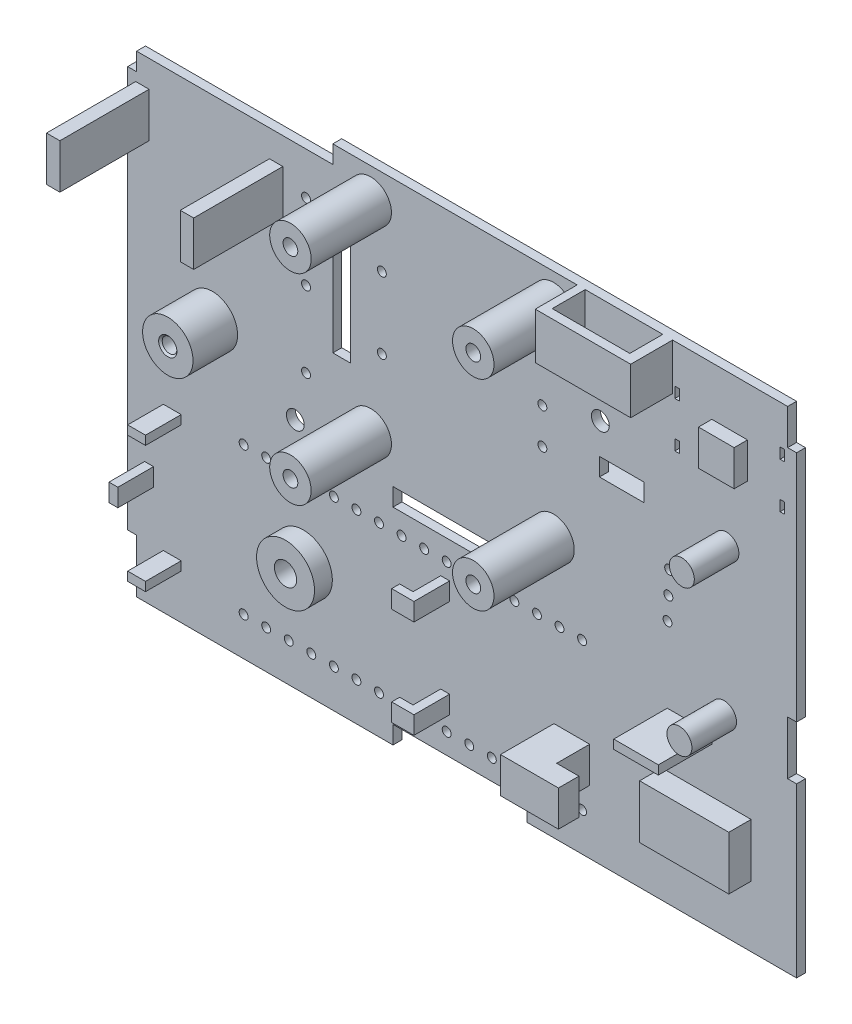
SolidWorks part; units mm, degrees
material "PLA"
ref_plane "前视基准面" through (0, 0, 0) normal (0, 0, 1) x (1, 0, 0)
ref_plane "上视基准面" through (0, 0, 0) normal (0, 1, 0) x (1, 0, 0)
ref_plane "右视基准面" through (0, 0, 0) normal (1, 0, 0) x (0, 0, -1)
sketch "草图1" plane through (0, 0, 0) normal (0, 0, 1) x (1, 0, 0)
  line L1 (-37.5, 27.5) -> (37.5, 27.5)
  line L2 (-37.5, 27.5) -> (-37.5, -27.5)
  line L3 (-37.5, -27.5) -> (37.5, -27.5)
  line L4 (37.5, 27.5) -> (37.5, -27.5)
  line L5 (-37.5, 27.5) -> (37.5, -27.5) construction
  line L6 (-37.5, -27.5) -> (37.5, 27.5) construction
  point P0 (0, 0)
  dimension "D1" = 55
  dimension "D2" = 75
extrude "凸台-拉伸1" add sketch "草图1" along normal blind 1
sketch "草图2" plane through (0, 0, 0) normal (0, 0, -1) x (-1, 0, 0)
  line L1 (-22.7477, 10.1) -> (-13.0477, 10.1)
  line L2 (-22.7477, 10.1) -> (-22.7477, 8.6)
  line L3 (-22.7477, 8.6) -> (-13.0477, 8.6)
  line L4 (-13.0477, 10.1) -> (-13.0477, 8.6)
  line L6 (31, -4.4) -> (-15.5, -4.4) construction
  line L7 (-14.1477, 1.6) -> (-14.1477, 8.6) construction
  line L8 (-21.6477, 1.6) -> (-21.6477, 8.6) construction
  dimension "D1" = 1.1
  dimension "D2" = 1.5
  dimension "D3" = 1.1
  dimension "D4" = 13
extrude "电源凸台-拉伸2" add sketch "草图2" along normal blind 7.1
sketch "草图4" plane through (0, 8.6, 0) normal (0, -1, 0) x (1, 0, 0)
  line L5 (16.1977, -2.8) -> (17.1977, -2.8)
  line L6 (16.1977, -2.8) -> (16.1977, -3.8)
  line L7 (16.1977, -3.8) -> (17.1977, -3.8)
  line L8 (17.1977, -2.8) -> (17.1977, -3.8)
  line L11 (17.8977, -7.1) -> (17.8977, 0) construction
  line L18 (22.7477, -7.1) -> (13.0477, -7.1) construction
  line L19 (-37.5, 0) -> (37.5, 0) construction
  line L20 (18.5977, -2.8) -> (18.5977, -3.8)
  line L21 (19.5977, -3.8) -> (18.5977, -3.8)
  line L22 (19.5977, -2.8) -> (19.5977, -3.8)
  line L23 (19.5977, -2.8) -> (18.5977, -2.8)
  dimension "D1" = 1
  dimension "D2" = 1
  dimension "D3" = 3.4
  dimension "D4" = 2.8
extrude "电源切除-拉伸1" cut sketch "草图4" against normal up to next
sketch "草图5" plane through (0, 0, 0) normal (0, 0, -1) x (-1, 0, 0)
  line L1 (-20.3977, 12.1) -> (-15.3977, 12.1)
  line L2 (-20.3977, 12.1) -> (-20.3977, 10.1)
  line L3 (-20.3977, 10.1) -> (-15.3977, 10.1)
  line L4 (-15.3977, 12.1) -> (-15.3977, 10.1)
  line L6 (-13.0477, 10.1) -> (-22.7477, 10.1) construction
  line L7 (-17.8977, 8.6) -> (-17.8977, 10.1) construction
  line L8 (-22.7477, 8.6) -> (-13.0477, 8.6) construction
  dimension "D1" = 2
  dimension "D2" = 5
extrude "电源线切除-拉伸2" cut sketch "草图5" against normal up to next
sketch "草图9" plane through (0, 0, 0) normal (0, 0, -1) x (-1, 0, 0)
  circle A3 centre (28, 3.6) radius 0.825
  dimension "D1" = 1.65
extrude "DH11拉伸-薄壁1" add sketch "草图9" along normal up to surface (5 mm away) from surface at -1 separate body thin
sketch "草图36" plane through (0, 0, 1) normal (0, 0, 1) x (1, 0, 0)
  line L0 (-21.7, -3.9) -> (-21.7, 24.5) construction
  line L1 (-21.6, 22.5) -> (-20.1, 22.5)
  line L2 (-21.6, 22.5) -> (-21.6, 17.5)
  line L3 (-21.6, 17.5) -> (-20.1, 17.5)
  line L4 (-20.1, 22.5) -> (-20.1, 17.5)
  line L5 (-36.6, 22.5) -> (-35.1, 22.5)
  line L6 (-36.6, 22.5) -> (-36.6, 17.5)
  line L7 (-36.6, 17.5) -> (-35.1, 17.5)
  line L8 (-35.1, 22.5) -> (-35.1, 17.5)
  line L9 (-21.7, 24.5) -> (-22.35, 24.5) construction
  line L10 (-35, 24.5) -> (-35, -3.9) construction
  dimension "D1" = 5
  dimension "D2" = 0.1
  dimension "D3" = 2
  dimension "D4" = 1.5
  dimension "D5" = 0.1
extrude "DH11凸台-拉伸11" add sketch "草图36" along normal blind 10
chamfer "HD11倒角3" distance 0.2 angle 45 1 edges at (-27.175, 3.6, 6)
sketch "草图13" plane through (0, 0, 0) normal (0, 0, -1) x (-1, 0, 0)
  line L0 (-24.35, 23.15) -> (-23.85, 23.15)
  line L1 (-36.15, 23.15) -> (-35.65, 23.15)
  line L2 (-36.15, 23.15) -> (-36.15, 21.95)
  line L3 (-36.15, 21.95) -> (-35.65, 21.95)
  line L4 (-35.65, 23.15) -> (-35.65, 21.95)
  line L7 (-24.35, 23.15) -> (-24.35, 21.95)
  line L8 (-24.35, 21.95) -> (-23.85, 21.95)
  line L9 (-23.85, 23.15) -> (-23.85, 21.95)
  line L10 (-24.35, 18.05) -> (-23.85, 18.05)
  line L11 (-24.35, 18.05) -> (-24.35, 16.85)
  line L12 (-24.35, 16.85) -> (-23.85, 16.85)
  line L13 (-23.85, 18.05) -> (-23.85, 16.85)
  line L14 (-36.15, 18.05) -> (-35.65, 18.05)
  line L15 (-36.15, 18.05) -> (-36.15, 16.85)
  line L16 (-36.15, 16.85) -> (-35.65, 16.85)
  line L17 (-35.65, 18.05) -> (-35.65, 16.85)
  line L18 (-36, 23) -> (-36, 22.1) construction
  line L19 (-35.8, 23) -> (-36, 23) construction
  dimension "D1" = 1.2
  dimension "D2" = 0.5
  dimension "D3" = 0.15
  dimension "D4" = 0.15
  dimension "D5" = 2
  dimension "D6" = 2
extrude "按键切除-拉伸3" cut sketch "草图13" against normal up to next (1 mm away)
sketch "草图35" plane through (0, 0, 0) normal (0, 0, -1) x (-1, 0, 0)
  line L0 (-35.65, 18.05) -> (-35.65, 21.95) construction
  line L1 (-32, 22) -> (-28, 22)
  line L2 (-32, 22) -> (-32, 18)
  line L3 (-32, 18) -> (-28, 18)
  line L4 (-28, 22) -> (-28, 18)
  line L5 (-30, 18.05) -> (-30, 23.8585) construction
  line L6 (-35.65, 18.05) -> (-24.35, 18.05) construction
  line L7 (-35.65, 20) -> (-24.0484, 20) construction
  line L8 (-24.35, 18.05) -> (-24.35, 16.85) construction
  point P11 (-30, 18.05)
  dimension "D1" = 4
  dimension "D2" = 4
extrude "按键凸台-拉伸10" add sketch "草图35" against normal up to surface (2.5 mm away)
sketch "草图18" plane through (0, 0, 0) normal (0, 0, -1) x (-1, 0, 0)
  circle A0 centre (17.8, -14.8882) radius 1.25
  dimension "D1" = 2.5
extrude "蜂鸣拉伸-薄壁9" add sketch "草图18" along normal up to surface (2 mm away) from surface at -1 separate body thin
sketch "草图38" plane through (0, 0, 1) normal (0, 0, 1) x (1, 0, 0)
  line L1 (-2.4, -8.3882) -> (-1.4, -8.3882)
  line L2 (-2.4, -8.3882) -> (-2.4, -10.3882)
  line L3 (-2.4, -10.3882) -> (-1.4, -10.3882)
  line L4 (-1.4, -8.3882) -> (-1.4, -10.3882)
  line L5 (-2.5, -8.3882) -> (-34.5, -8.3882) construction
  line L6 (-2.5, -21.3882) -> (-2.5, -8.3882) construction
  line L7 (-2.5, -14.8882) -> (3.3991, -14.8882) construction
  line L8 (-1.4, -21.3882) -> (-1.4, -19.3882)
  line L9 (-2.4, -19.3882) -> (-1.4, -19.3882)
  line L10 (-2.4, -21.3882) -> (-2.4, -19.3882)
  line L11 (-2.4, -21.3882) -> (-1.4, -21.3882)
  line L12 (-34.5, -14.8882) -> (-26.3035, -14.8882) construction
  line L13 (-33.5, -7.2882) -> (-31.5, -7.2882)
  line L14 (-33.5, -7.2882) -> (-33.5, -8.2882)
  line L15 (-33.5, -8.2882) -> (-31.5, -8.2882)
  line L16 (-31.5, -7.2882) -> (-31.5, -8.2882)
  line L17 (-34.5, -8.3882) -> (-34.5, -14.8882) construction
  line L18 (-31.5, -22.4882) -> (-31.5, -21.4882)
  line L19 (-33.5, -21.4882) -> (-31.5, -21.4882)
  line L20 (-33.5, -22.4882) -> (-33.5, -21.4882)
  line L21 (-33.5, -22.4882) -> (-31.5, -22.4882)
  line L23 (-35.6, -13.895) -> (-34.6, -13.895)
  line L24 (-35.6, -13.895) -> (-35.6, -15.895)
  line L25 (-35.6, -15.895) -> (-34.6, -15.895)
  line L26 (-34.6, -13.895) -> (-34.6, -15.895)
  dimension "D1" = 1
  dimension "D2" = 2
  dimension "D3" = 0
  dimension "D4" = 0.1
  dimension "D5" = 2
  dimension "D6" = 1
  dimension "D7" = 0.1
  dimension "D8" = 1
  dimension "D9" = 0.1
  dimension "D10" = 2
  dimension "D11" = 1
extrude "蜂鸣凸台-拉伸12" add sketch "草图38" along normal blind 4
sketch "草图20" plane through (0, 0, 0) normal (0, 0, -1) x (-1, 0, 0)
  line L3 (-23.6, 22.3) -> (-12.9, 22.3)
  line L5 (-24, 26) -> (-24, 14) construction
  line L7 (-37.5, 27.5) -> (37.5, 27.5) construction
  line L8 (-23.6, 27.5) -> (-12.9, 27.5)
  line L10 (-23.6, 27.5) -> (-23.6, 22.3)
  line L11 (-12.9, 27.5) -> (-12.9, 22.3)
  dimension "D1" = 5.2
  dimension "D2" = 10.7
  dimension "D6" = 0.4
extrude "开关凸台-拉伸6" add sketch "草图20" against normal blind 4.7 from surface at -1 starting at face at (30, 20, 1)
sketch "草图37" plane through (0, 27.5, 0) normal (0, 1, 0) x (1, 0, 0)
  line L0 (23.6, -5.7) -> (12.9, -5.7) construction
  line L1 (13.8, -1) -> (22.5, -1)
  line L2 (13.8, -1) -> (13.8, -4.7)
  line L3 (13.8, -4.7) -> (22.5, -4.7)
  line L4 (22.5, -1) -> (22.5, -4.7)
  line L5 (12.9, -5.7) -> (12.9, -1) construction
  dimension "D1" = 3.7
  dimension "D2" = 8.7
  dimension "D3" = 1
  dimension "D4" = 0.9
extrude "开关1切除-拉伸10" cut sketch "草图37" against normal blind 4
sketch "草图34" plane through (0, 22.3, 0) normal (0, -1, 0) x (1, 0, 0)
  line L1 (15.9, 2.9) -> (15.9, 2.6) construction
  line L2 (15.3, 3) -> (16, 3)
  line L3 (15.3, 3) -> (15.3, 2.5)
  line L4 (15.3, 2.5) -> (16, 2.5)
  line L5 (16, 3) -> (16, 2.5)
  line L6 (15.9, 2.6) -> (15.4, 2.6) construction
  line L8 (15.4, 2.6) -> (15.4, 2.9) construction
  line L9 (15.4, 2.9) -> (15.9, 2.9) construction
  line L10 (17.8, 3) -> (18.5, 3)
  line L11 (17.8, 3) -> (17.8, 2.5)
  line L12 (17.8, 2.5) -> (18.5, 2.5)
  line L13 (18.5, 3) -> (18.5, 2.5)
  line L14 (20.3, 3) -> (21, 3)
  line L15 (20.3, 3) -> (20.3, 2.5)
  line L16 (20.3, 2.5) -> (21, 2.5)
  line L17 (21, 3) -> (21, 2.5)
  dimension "D1" = 0.1
  dimension "D2" = 0.1
  dimension "D3" = 0.1
  dimension "D4" = 0.1
  dimension "D5" = 3
extrude "开关底切除-拉伸10" cut sketch "草图34" against normal up to next (1.2 mm away)
sketch "草图28" plane through (0, 0, 1) normal (0, 0, 1) x (1, 0, 0)
  circle A0 centre (29.6356, 10.4762) radius 1.4
  circle A2 centre (29.3644, -6.0215) radius 1.4
extrude "红外凸台-拉伸11" add sketch "草图28" along normal blind 5
sketch "草图19" plane through (0, 0, 0) normal (0, 0, -1) x (-1, 0, 0)
  circle A3 centre (-23.0325, -0.0809) radius 0.5
  circle A4 centre (-23.1241, 2.4574) radius 0.5
  circle A5 centre (-23.2157, 4.9958) radius 0.5
extrude "红外切除-拉伸4" cut sketch "草图19" against normal up to next (1 mm away)
sketch "草图30" plane through (0, 0, 0) normal (0, 0, -1) x (-1, 0, 0)
  line L0 (-37.5, 27.5) -> (37.5, 27.5) construction
  line L1 (36.5, 27.5) -> (37.5, 27.5)
  line L2 (36.5, 27.5) -> (36.5, 23.5)
  line L3 (36.5, 23.5) -> (37.5, 23.5)
  line L4 (37.5, 27.5) -> (37.5, 23.5)
  line L5 (37.5, 27.5) -> (37.5, -27.5) construction
  line L7 (36.5, -21.5) -> (37.5, -21.5)
  line L8 (36.5, -21.5) -> (36.5, -27.5)
  line L9 (36.5, -27.5) -> (37.5, -27.5)
  line L10 (37.5, -21.5) -> (37.5, -27.5)
  line L11 (-37.5, -2.65) -> (-36.5, -2.65)
  line L12 (-37.5, -2.65) -> (-37.5, -8.65)
  line L13 (-37.5, -8.65) -> (-36.5, -8.65)
  line L14 (-36.5, -2.65) -> (-36.5, -8.65)
  line L15 (37.5, -27.5) -> (-37.5, -27.5) construction
  line L17 (-37.5, 27.5) -> (-36.5, 27.5)
  line L18 (-37.5, 27.5) -> (-37.5, 23.5)
  line L19 (-37.5, 23.5) -> (-36.5, 23.5)
  line L20 (-36.5, 27.5) -> (-36.5, 23.5)
  line L21 (-37.5, -27.5) -> (-37.5, 27.5) construction
  line L22 (-39.4, -5.65) -> (-36.1685, -5.65) construction
  dimension "D1" = 4
  dimension "D2" = 1
  dimension "D3" = 6
extrude "螺丝孔切除-拉伸9" cut sketch "草图30" against normal up to surface (1 mm away) up to face at (23.5325, -0.0809, 1)
sketch "草图33" plane through (0, 0, 1) normal (0, 0, 1) x (1, 0, 0)
  line L0 (0, 26.35) -> (0, 1.95) construction
  line L1 (12.5, 26.35) -> (-12.5, 26.35) construction
  line L2 (7, 1.95) -> (-7, 1.95) construction
  circle A0 centre (-10.25, 24.1) radius 1.45 construction
  circle A1 centre (-10.25, 24.1) radius 1.45 construction
  circle A2 centre (-10.25, 24.1) radius 0.825
  circle A3 centre (10.25, 24.1) radius 0.825
  circle A4 centre (-10.25, 1.6) radius 0.825
  circle A5 centre (10.25, 1.6) radius 0.825
  dimension "D1" = 1.65
  dimension "D2" = 1.65
extrude "屏幕拉伸-薄壁10" add sketch "草图33" along normal up to surface (9 mm away) separate body thin
sketch "草图39" plane through (0, 0, 1) normal (0, 0, 1) x (1, 0, 0)
  line L0 (14.4, -23.4) -> (14.4, -13.4) construction
  line L1 (10.3, -16.4) -> (14.3, -16.4)
  line L2 (10.3, -16.4) -> (10.3, -20.4)
  line L3 (10.3, -20.4) -> (14.3, -20.4)
  line L4 (14.3, -16.4) -> (14.3, -20.4)
  line L6 (14.4, -13.4) -> (13, -13.4) construction
  line L7 (41, -9.65) -> (13, -9.65) construction
  line L8 (23, -8.55) -> (28, -8.55)
  line L9 (23, -8.55) -> (23, -9.55)
  line L10 (23, -9.55) -> (28, -9.55)
  line L11 (28, -8.55) -> (28, -9.55)
  line L12 (13, -9.65) -> (13, -13.4) construction
  point P10 (13.7, -13.4)
  dimension "D1" = 0.1
  dimension "D2" = 4
  dimension "D3" = 4
  dimension "D4" = 3
  dimension "D5" = 0.1
  dimension "D6" = 5
  dimension "D7" = 1
  dimension "D8" = 10
extrude "充电板凸台-拉伸2" add sketch "草图39" along normal blind 6
sketch "草图40" plane through (0, 0, 1) normal (0, 0, 1) x (1, 0, 0)
  line L1 (41, -9.65) -> (13, -9.65) construction
  line L2 (22.4, -14.65) -> (32.4, -14.65)
  line L3 (22.4, -14.65) -> (22.4, -20.65)
  line L4 (22.4, -20.65) -> (32.4, -20.65)
  line L5 (32.4, -14.65) -> (32.4, -20.65)
  line L6 (14.4, -23.4) -> (14.4, -13.4) construction
  dimension "D1" = 6
  dimension "D2" = 10
  dimension "D3" = 5
  dimension "D4" = 8
extrude "充电楹凸台-拉伸3" add sketch "草图40" along normal up to surface (2.5 mm away)
sketch "草图41" plane through (0, 0, 1) normal (0, 0, 1) x (1, 0, 0)
  circle A8 centre (-24.5, -23.2) radius 0.5 construction
  circle A9 centre (-21.97, -23.2) radius 0.5 construction
  circle A10 centre (-19.44, -23.2) radius 0.5 construction
  circle A11 centre (-16.91, -23.2) radius 0.5 construction
  circle A12 centre (-14.38, -23.2) radius 0.5 construction
  circle A13 centre (-11.85, -23.2) radius 0.5 construction
  circle A14 centre (-9.32, -23.2) radius 0.5 construction
  circle A15 centre (-6.79, -23.2) radius 0.5 construction
  circle A16 centre (-4.26, -23.2) radius 0.5 construction
  circle A17 centre (-1.73, -23.2) radius 0.5 construction
  circle A18 centre (0.8, -23.2) radius 0.5 construction
  circle A19 centre (3.33, -23.2) radius 0.5 construction
  circle A20 centre (5.86, -23.2) radius 0.5 construction
  circle A21 centre (8.39, -23.2) radius 0.5 construction
  circle A22 centre (10.92, -23.2) radius 0.5 construction
  circle A23 centre (13.45, -23.2) radius 0.5 construction
  circle A24 centre (13.45, -6.7) radius 0.5 construction
  circle A25 centre (10.92, -6.7) radius 0.5 construction
  circle A26 centre (8.39, -6.7) radius 0.5 construction
  circle A27 centre (5.86, -6.7) radius 0.5 construction
  circle A28 centre (3.33, -6.7) radius 0.5 construction
  circle A29 centre (0.8, -6.7) radius 0.5 construction
  circle A30 centre (-1.73, -6.7) radius 0.5 construction
  circle A31 centre (-4.26, -6.7) radius 0.5 construction
  circle A32 centre (-6.79, -6.7) radius 0.5 construction
  circle A33 centre (-9.32, -6.7) radius 0.5 construction
  circle A34 centre (-11.85, -6.7) radius 0.5 construction
  circle A35 centre (-14.38, -6.7) radius 0.5 construction
  circle A36 centre (-16.91, -6.7) radius 0.5 construction
  circle A37 centre (-19.44, -6.7) radius 0.5 construction
  circle A38 centre (-21.97, -6.7) radius 0.5 construction
  circle A39 centre (-24.5, -6.7) radius 0.5 construction
  circle A40 centre (-24.5, -23.2) radius 0.5
  circle A41 centre (-21.97, -23.2) radius 0.5
  circle A42 centre (-19.44, -23.2) radius 0.5
  circle A43 centre (-16.91, -23.2) radius 0.5
  circle A44 centre (-14.38, -23.2) radius 0.5
  circle A45 centre (-11.85, -23.2) radius 0.5
  circle A46 centre (-9.32, -23.2) radius 0.5
  circle A47 centre (-6.79, -23.2) radius 0.5
  circle A48 centre (-4.26, -23.2) radius 0.5
  circle A49 centre (-1.73, -23.2) radius 0.5
  circle A50 centre (0.8, -23.2) radius 0.5
  circle A51 centre (3.33, -23.2) radius 0.5
  circle A52 centre (5.86, -23.2) radius 0.5
  circle A53 centre (8.39, -23.2) radius 0.5
  circle A54 centre (10.92, -23.2) radius 0.5
  circle A55 centre (13.45, -23.2) radius 0.5
  circle A56 centre (13.45, -6.7) radius 0.5
  circle A57 centre (10.92, -6.7) radius 0.5
  circle A58 centre (8.39, -6.7) radius 0.5
  circle A59 centre (5.86, -6.7) radius 0.5
  circle A60 centre (3.33, -6.7) radius 0.5
  circle A61 centre (0.8, -6.7) radius 0.5
  circle A62 centre (-1.73, -6.7) radius 0.5
  circle A63 centre (-4.26, -6.7) radius 0.5
  circle A64 centre (-6.79, -6.7) radius 0.5
  circle A65 centre (-9.32, -6.7) radius 0.5
  circle A66 centre (-11.85, -6.7) radius 0.5
  circle A67 centre (-14.38, -6.7) radius 0.5
  circle A68 centre (-16.91, -6.7) radius 0.5
  circle A69 centre (-19.44, -6.7) radius 0.5
  circle A70 centre (-21.97, -6.7) radius 0.5
  circle A71 centre (-24.5, -6.7) radius 0.5
  circle A72 centre (9, 9.85) radius 0.5 construction
  circle A73 centre (9, 13.85) radius 0.5 construction
  circle A74 centre (-9, 17.85) radius 0.5 construction
  circle A75 centre (-9, 9.85) radius 0.5 construction
  circle A76 centre (9, 9.85) radius 0.5
  circle A77 centre (9, 13.85) radius 0.5
  circle A78 centre (-9, 17.85) radius 0.5
  circle A79 centre (-9, 9.85) radius 0.5
extrude "零件孔切除-拉伸10" cut sketch "草图41" against normal up to next (1 mm away)
sketch "草图42" plane through (0, 0, 0) normal (0, 0, -1) x (-1, 0, 0)
  circle A4 centre (-15.5, 15.6) radius 1
  circle A5 centre (18.7, -1.4) radius 1
  dimension "D1" = 2
  dimension "D2" = 2
extrude "固定孔切除-拉伸11" cut sketch "草图42" against normal up to next (1 mm away)
sketch "草图43" plane through (0, 0, 0) normal (0, 0, -1) x (-1, 0, 0)
  line L0 (31, -4.4) -> (-15.5, -4.4) construction
  line L1 (-7.25, -2.4) -> (7.75, -2.4)
  line L2 (-7.25, -2.4) -> (-7.25, -4.4)
  line L3 (-7.25, -4.4) -> (7.75, -4.4)
  line L4 (7.75, -2.4) -> (7.75, -4.4)
  line L5 (-15.5, -25.5) -> (31, -25.5) construction
  line L6 (-7.25, -25.5) -> (7.75, -25.5)
  line L7 (-7.25, -25.5) -> (-7.25, -27.5)
  line L8 (-7.25, -27.5) -> (7.75, -27.5)
  line L9 (7.75, -25.5) -> (7.75, -27.5)
  line L10 (36.5, -27.5) -> (-37.5, -27.5) construction
  line L11 (12.5, 26.35) -> (12.5, -0.65) construction
  line L12 (12.5, 21.1) -> (14.5, 21.1)
  line L13 (12.5, 21.1) -> (12.5, 7.2)
  line L14 (12.5, 7.2) -> (14.5, 7.2)
  line L15 (14.5, 21.1) -> (14.5, 7.2)
  line L16 (-12.5, 7.2) -> (12.5, 7.2) construction
  line L17 (12.5, 21.1) -> (-12.5, 21.1) construction
  line L18 (-36.5, 27.5) -> (36.5, 27.5) construction
  line L19 (36.5, 27.5) -> (36.5, 23.5) construction
  line L20 (14.5, 27.5) -> (36.5, 27.5)
  line L21 (14.5, 27.5) -> (14.5, 25.5)
  line L22 (14.5, 25.5) -> (36.5, 25.5)
  line L23 (36.5, 27.5) -> (36.5, 25.5)
  dimension "D1" = 2
  dimension "D2" = 15
  dimension "D3" = 2
extrude "走线切口切除-拉伸1" cut sketch "草图43" against normal up to next (1 mm away)
sketch "草图44" plane through (0, 0, 0) normal (0, 0, -1) x (-1, 0, 0)
  line L0 (17.425, 20.75) -> (17.575, 20.75) construction
  line L1 (17.425, 12.25) -> (17.575, 12.25) construction
  line L2 (17.425, 3.75) -> (17.575, 3.75) construction
  line L3 (17.425, 20.75) -> (17.425, 19.5) construction
  line L4 (17.575, 19.5) -> (17.575, 20.75) construction
  circle A1 centre (17.5, 20.75) radius 0.5
  circle A2 centre (17.5, 12.25) radius 0.5
  circle A3 centre (17.5, 3.75) radius 0.5
  dimension "D1" = 1
  dimension "D2" = 3
extrude "电阻切除-拉伸1" cut sketch "草图44" against normal up to next (1 mm away)
sketch "草图45" plane through (0, 0, 0) normal (0, 0, -1) x (-1, 0, 0)
  line L0 (-7.25, -27.5) -> (-37.5, -27.5) construction
  line L1 (-21.6, -13.5) -> (-20.1, -13.5)
  line L2 (-21.6, -13.5) -> (-21.6, -16.5)
  line L3 (-21.6, -16.5) -> (-20.1, -16.5)
  line L4 (-20.1, -13.5) -> (-20.1, -16.5)
  line L9 (-7.25, -25.5) -> (-7.25, -27.5) construction
  line L14 (-18, -2.8) -> (-13, -2.8)
  line L15 (-18, -2.8) -> (-18, -4.3)
  line L16 (-18, -4.3) -> (-13, -4.3)
  line L17 (-13, -2.8) -> (-13, -4.3)
  line L22 (-20, -12.84) -> (-20, -14.95) construction
  line L23 (-20, -25.5) -> (-17.7826, -25.5) construction
  line L24 (31, -4.4) -> (-15.5, -4.4) construction
  line L25 (-20, -4.4) -> (-20, -6.51) construction
  line L26 (9, -2.8) -> (14, -2.8)
  line L27 (9, -2.8) -> (9, -4.3)
  line L28 (9, -4.3) -> (14, -4.3)
  line L29 (14, -2.8) -> (14, -4.3)
  line L30 (9, -25.6) -> (14, -25.6)
  line L31 (9, -25.6) -> (9, -27.1)
  line L32 (9, -27.1) -> (14, -27.1)
  line L33 (14, -25.6) -> (14, -27.1)
  line L34 (-18, -25.6) -> (-13, -25.6)
  line L35 (-18, -25.6) -> (-18, -27.1)
  line L36 (-18, -27.1) -> (-13, -27.1)
  line L37 (-13, -25.6) -> (-13, -27.1)
  dimension "D1" = 0.1
  dimension "D2" = 3
  dimension "D3" = 12
  dimension "D4" = 1.5
  dimension "D5" = 5
  dimension "D6" = 1.5
  dimension "D7" = 0.1
  dimension "D8" = 2
  dimension "D11" = 0.4
  dimension "D12" = 5.75
  dimension "D9" = 2
  dimension "D10" = 2
extrude "ESP32固定凸台-拉伸2" add sketch "草图45" along normal blind 1
sketch "草图46" plane through (14.3, 0, 0) normal (1, 0, 0) x (0, 0, -1)
  line L1 (-7, -16.4) -> (-4.7, -16.4)
  line L2 (-7, -16.4) -> (-7, -20.4)
  line L3 (-7, -20.4) -> (-4.7, -20.4)
  line L4 (-4.7, -16.4) -> (-4.7, -20.4)
  line L6 (-4.5, -22.9) -> (-4.5, -13.9) construction
  line L9 (-7, -20.4) -> (-1, -20.4) construction
  line L10 (-7, -16.4) -> (-1, -16.4) construction
  dimension "D1" = 0.2
  dimension "D2" = 2.3
extrude "充电板固定凸台-拉伸3" add sketch "草图46" along normal blind 2.5
sketch "草图47" plane through (-2.4, 0, 0) normal (-1, 0, 0) x (0, 0, 1)
  line L0 (5, -19.3882) -> (1, -19.3882) construction
  line L1 (4.1, -19.3882) -> (5, -19.3882)
  line L2 (4.1, -19.3882) -> (4.1, -21.3882)
  line L3 (4.1, -21.3882) -> (5, -21.3882)
  line L4 (5, -19.3882) -> (5, -21.3882)
  line L5 (4, -14.8882) -> (4, -21.3882) construction
  line L13 (5, -8.3882) -> (1, -8.3882) construction
  line L14 (4.1, -8.3882) -> (5, -8.3882)
  line L15 (4.1, -8.3882) -> (4.1, -10.3882)
  line L16 (4.1, -10.3882) -> (5, -10.3882)
  line L17 (5, -8.3882) -> (5, -10.3882)
  line L18 (4, -8.3882) -> (4, -14.8882) construction
  dimension "D1" = 0.1
  dimension "D3" = 0.1
extrude "蜂鸣固定凸台-拉伸2" add sketch "草图47" along normal blind 1.5
sketch "草图48" plane through (0, 8.6, 0) normal (0, -1, 0) x (1, 0, 0)
  line L4 (22.7477, 0) -> (13.0477, 0)
  line L5 (13.0477, 0) -> (13.0477, -7.1)
  line L6 (13.0477, -7.1) -> (22.7477, -7.1)
  line L7 (22.7477, -7.1) -> (22.7477, 0)
  line L8 (22.7477, 0) -> (13.0477, 0)
  line L9 (13.0477, 0) -> (13.0477, -7.1)
  line L10 (13.0477, -7.1) -> (22.7477, -7.1)
  line L11 (22.7477, -7.1) -> (22.7477, 0)
  dimension "D1" = 0
extrude "电源接口凸台-拉伸2" add sketch "草图48" along normal blind 3
sketch "草图49" plane through (0, 5.6, 0) normal (0, -1, 0) x (1, 0, 0)
  line L1 (14.0477, 0) -> (21.7477, 0)
  line L2 (14.0477, 0) -> (14.0477, -6.1)
  line L3 (14.0477, -6.1) -> (21.7477, -6.1)
  line L4 (21.7477, 0) -> (21.7477, -6.1)
  line L5 (21.6477, -6) -> (21.6477, 0) construction
  line L6 (19.8977, -6) -> (21.6477, -6) construction
  line L7 (14.1477, 0) -> (14.1477, -6) construction
  line L8 (7.25, 0) -> (37.5, 0) construction
  dimension "D1" = 0.1
  dimension "D2" = 0.1
  dimension "D3" = 0.1
extrude "切除-拉伸1" cut sketch "草图49" against normal blind 3
